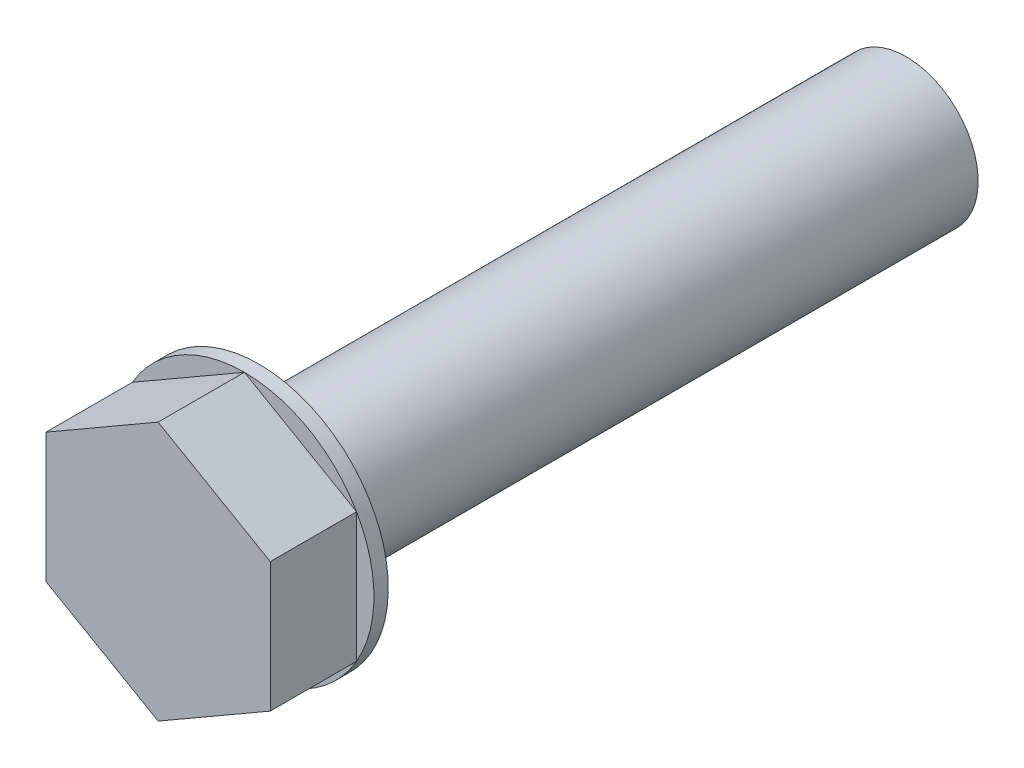
SolidWorks part; units mm, degrees
material "AISI 4340 Steel, normalized"
ref_plane "Front Plane" through (0, 0, 0) normal (0, 0, 1) x (1, 0, 0)
ref_plane "Top Plane" through (0, 0, 0) normal (0, 1, 0) x (1, 0, 0)
ref_plane "Right Plane" through (0, 0, 0) normal (1, 0, 0) x (0, 0, -1)
sketch "Sketch1" plane through (0, 0, 0) normal (0, 0, 1) x (1, 0, 0)
  line L1 (0, 9) -> (-7.7942, 4.5)
  line L2 (-7.7942, 4.5) -> (-7.7942, -4.5)
  line L3 (-7.7942, -4.5) -> (0, -9)
  line L4 (0, -9) -> (7.7942, -4.5)
  line L5 (7.7942, -4.5) -> (7.7942, 4.5)
  line L6 (7.7942, 4.5) -> (0, 9)
  circle A1 centre (0, 0) radius 7.7942 construction
extrude "Boss-Extrude1" add sketch "Sketch1" along normal blind 6
sketch "Sketch2" plane through (0, 0, 0) normal (0, 0, -1) x (-1, 0, 0)
  circle A0 centre (0, 0) radius 9
extrude "Boss-Extrude2" add sketch "Sketch2" along normal blind 1
sketch "Sketch3" plane through (0, 0, -1) normal (0, 0, -1) x (-1, 0, 0)
  circle A0 centre (0, 0) radius 5
extrude "Boss-Extrude3" add sketch "Sketch3" along normal blind 45
